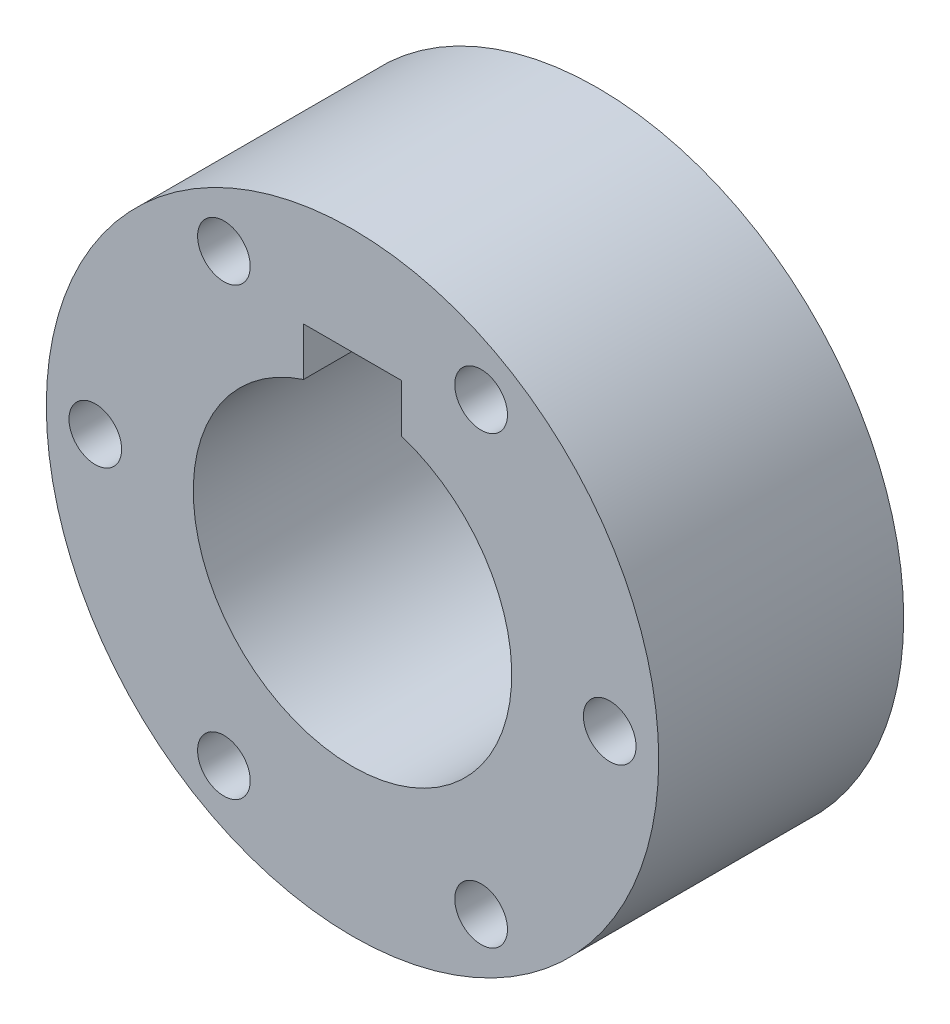
SolidWorks part; units mm, degrees
material "1.7225 (42CrMo4)"
ref_plane "Alzado" through (0, 0, 0) normal (0, 0, 1) x (1, 0, 0)
ref_plane "Planta" through (0, 0, 0) normal (0, 1, 0) x (1, 0, 0)
ref_plane "Vista lateral" through (0, 0, 0) normal (1, 0, 0) x (0, 0, -1)
sketch "Croquis1" plane through (0, 0, 0) normal (0, 0, 1) x (1, 0, 0)
  circle A0 centre (0, 0) radius 25
  dimension "D1" = 50
extrude "Saliente-Extruir1" add sketch "Croquis1" along normal blind 20
sketch "KeySketch" plane through (-0.3586, -1.1713, 20) normal (0, 0, 1) x (1, 0, 0)
  line L0 (0.3586, -11.8287) -> (0.3586, 17.4713) construction
  line L1 (-12.6414, 1.1713) -> (13.3586, 1.1713) construction
  line L2 (-3.6414, 13.5406) -> (-3.6414, 17.4713)
  line L4 (4.3586, 17.4713) -> (4.3586, 13.5406)
  line L5 (4.3586, 17.4713) -> (-3.6414, 17.4713)
  arc A0 (-3.6414, 13.5406) -> (4.3586, 13.5406) centre (0.3586, 1.1713) ccw
  circle A1 centre (0.3586, 1.1713) radius 25 construction
  point P10 (0.3586, 17.4713)
  dimension "Diameter" = 26
  dimension "Width" = 8
  dimension "Depth" = 3.3
extrude "Keyway" cut sketch "KeySketch" against normal through all
other "bore with deep pattern keyway din 6886 p1<1>"
hole_wizard "Taladro de margen para M41" positions "Croquis11" profile "Croquis10" hole size "M4" standard "ISO" end condition through all
sketch "Croquis11" plane through (0, 0, 20) normal (0, 0, 1) x (1, 0, 0)
  point P0 (21, 0)
  point P14 (10.5, -18.1865)
  point P15 (-10.5, -18.1865)
  point P16 (-21, 0)
  point P17 (-10.5, 18.1865)
  point P18 (10.5, 18.1865)
  dimension "D1" = 21
  dimension "D2" = 6
sketch "Croquis10" plane through (21, 0, 20) normal (1, 0, 0) x (0, -1, 0)
  line L0 (0, 0) -> (0, 20)
  line L1 (0, 20) -> (2.15, 20)
  line L2 (2.15, 20) -> (2.15, 0)
  line L5 (2.15, 0) -> (0, 0)
  line L11 (0, -6.35) -> (0, 107.95) construction
  dimension "Diámetro de taladro hasta el siguiente" = 4.3
  dimension "Profundidad de taladro hasta el siguiente" = 20
